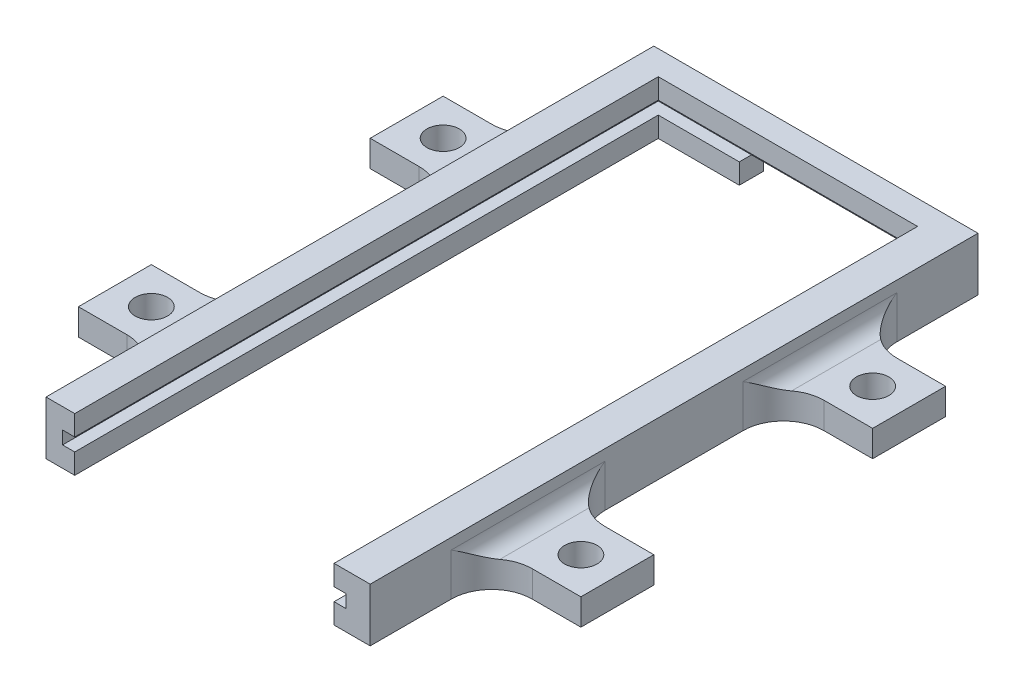
SolidWorks part; units mm, degrees
ref_plane "Front Plane" through (0, 0, 0) normal (0, 0, 1) x (1, 0, 0)
ref_plane "Top Plane" through (0, 0, 0) normal (0, 1, 0) x (1, 0, 0)
ref_plane "Right Plane" through (0, 0, 0) normal (1, 0, 0) x (0, 0, -1)
sketch "Sketch2" plane through (0, 0, 0) normal (0, 0, 1) x (1, 0, 0)
  line L1 (-20.1398, -2.4559) -> (19.8602, -2.4559)
  line L2 (-20.1398, -2.4559) -> (-20.1398, 4.1441)
  line L3 (-20.1398, 4.1441) -> (19.8602, 4.1441)
  line L4 (19.8602, -2.4559) -> (19.8602, 4.1441)
  point P0 (0, 0)
  dimension "D1" = 40
  dimension "D2" = 6.6
extrude "Boss-Extrude1" add sketch "Sketch2" along normal blind 3
sketch "Sketch3" plane through (0, 0, 3) normal (0, 0, 1) x (1, 0, 0)
  line L0 (-20.1398, -2.4559) -> (19.8602, -2.4559) construction
  line L1 (-18.0939, 1.6441) -> (16.9061, 1.6441)
  line L2 (-18.0939, 1.6441) -> (-18.0939, 0.0441)
  line L3 (-18.0939, 0.0441) -> (16.9061, 0.0441)
  line L4 (16.9061, 1.6441) -> (16.9061, 0.0441)
  point P0 (0, 0.8766)
  dimension "D1" = 35
  dimension "D2" = 1.6
  dimension "D3" = 2.5
extrude "Cut-Extrude1" cut sketch "Sketch3" against normal blind 1.5
sketch "Sketch4" plane through (0, 0, 3) normal (0, 0, 1) x (1, 0, 0)
  line L0 (-16.5939, 4.1441) -> (-20.1398, 4.1441)
  line L1 (19.8602, 4.1441) -> (-20.1398, 4.1441) construction
  line L2 (-20.1398, 4.1441) -> (-20.1398, -2.4559)
  line L3 (-20.1398, -2.4559) -> (-16.5939, -2.4559)
  line L4 (-20.1398, -2.4559) -> (19.8602, -2.4559) construction
  line L5 (-16.5939, -2.4559) -> (-16.5939, 0.0441)
  line L6 (-18.0939, 0.0441) -> (16.9061, 0.0441) construction
  line L7 (-16.5939, 0.0441) -> (-18.0939, 0.0441)
  line L8 (-18.0939, 0.0441) -> (-18.0939, 1.6441)
  line L9 (-18.0939, 1.6441) -> (-16.5939, 1.6441)
  line L10 (16.9061, 1.6441) -> (-18.0939, 1.6441) construction
  line L11 (-16.5939, 1.6441) -> (-16.5939, 4.1441)
  line L12 (15.4061, 4.1441) -> (15.4061, 1.6441)
  line L13 (15.4061, 1.6441) -> (16.9061, 1.6441)
  line L14 (16.9061, 1.6441) -> (16.9061, 0.0441)
  line L15 (16.9061, 0.0441) -> (15.4061, 0.0441)
  line L16 (-18.0939, 0.0441) -> (16.9061, 0.0441) construction
  line L17 (15.4061, 0.0441) -> (15.4061, -2.4559)
  line L18 (15.4061, -2.4559) -> (19.8602, -2.4559)
  line L19 (19.8602, -2.4559) -> (19.8602, 4.1441)
  line L20 (19.8602, 4.1441) -> (15.4061, 4.1441)
  dimension "D1" = 1.5
  dimension "D2" = 1.5
extrude "Boss-Extrude2" add sketch "Sketch4" along normal blind 72
sketch "Sketch5" plane through (0, 0, 3) normal (0, 0, 1) x (1, 0, 0)
  line L0 (-16.5939, 0.0441) -> (15.4061, 0.0441) construction
  line L1 (-6.5939, 0.0441) -> (15.4061, 0.0441)
  line L2 (-6.5939, 0.0441) -> (-6.5939, -2.4559)
  line L3 (-6.5939, -2.4559) -> (15.4061, -2.4559)
  line L4 (15.4061, 0.0441) -> (15.4061, -2.4559)
  line L5 (15.4061, 0.0441) -> (15.4061, -2.4559) construction
  line L6 (-16.5939, -2.4559) -> (15.4061, -2.4559) construction
  dimension "D1" = 22
extrude "Cut-Extrude2" cut sketch "Sketch5" against normal blind 4
sketch "Sketch6" plane through (-20.1398, 0, 0) normal (-1, 0, 0) x (0, 0, 1)
  line L0 (75, -2.4559) -> (0, -2.4559) construction
  line L1 (15, 0.7941) -> (24, 0.7941)
  line L2 (15, 0.7941) -> (15, -2.4559)
  line L3 (15, -2.4559) -> (24, -2.4559)
  line L4 (24, 0.7941) -> (24, -2.4559)
  line L5 (0, 4.1441) -> (0, -2.4559) construction
  line L6 (51, 0.7941) -> (60, 0.7941)
  line L7 (51, 0.7941) -> (51, -2.4559)
  line L8 (51, -2.4559) -> (60, -2.4559)
  line L9 (60, 0.7941) -> (60, -2.4559)
  line L10 (75, 4.1441) -> (75, -2.4559) construction
  dimension "D1" = 9
  dimension "D2" = 3.25
  dimension "D3" = 15
  dimension "D4" = 15
extrude "Boss-Extrude3" add sketch "Sketch6" along normal blind 11
sketch "Sketch7" plane through (19.8602, 0, 0) normal (1, 0, 0) x (0, 0, -1)
  line L0 (-75, -2.4559) -> (0, -2.4559) construction
  line L1 (-60, 0.7941) -> (-51, 0.7941)
  line L2 (-60, 0.7941) -> (-60, -2.4559)
  line L3 (-60, -2.4559) -> (-51, -2.4559)
  line L4 (-51, 0.7941) -> (-51, -2.4559)
  line L5 (-75, -2.4559) -> (-75, 4.1441) construction
  line L6 (-24, 0.7941) -> (-15, 0.7941)
  line L7 (-24, 0.7941) -> (-24, -2.4559)
  line L8 (-24, -2.4559) -> (-15, -2.4559)
  line L9 (-15, 0.7941) -> (-15, -2.4559)
  line L10 (0, -2.4559) -> (0, 4.1441) construction
  dimension "D1" = 9
  dimension "D2" = 3.25
  dimension "D3" = 15
  dimension "D4" = 15
extrude "Boss-Extrude4" add sketch "Sketch7" along normal blind 11
sketch "Sketch8" plane through (0, 0.7941, 0) normal (0, 1, 0) x (1, 0, 0)
  line L0 (-31.1398, -15) -> (-20.1398, -15) construction
  line L1 (-31.1398, -24) -> (-31.1398, -15) construction
  line L2 (-31.1398, -51) -> (-20.1398, -51) construction
  line L3 (-31.1398, -60) -> (-31.1398, -51) construction
  line L4 (30.8602, -15) -> (19.8602, -15) construction
  line L5 (30.8602, -15) -> (30.8602, -24) construction
  line L6 (30.8602, -51) -> (19.8602, -51) construction
  line L8 (30.8602, -51) -> (30.8602, -60) construction
  circle A0 centre (-26.6398, -19.5) radius 2
  circle A1 centre (-26.6398, -55.5) radius 2
  circle A2 centre (26.3602, -55.5) radius 2
  circle A3 centre (26.3602, -19.5) radius 2
  dimension "D1" = 4
  dimension "D4" = 4
  dimension "D5" = 4
  dimension "D6" = 4
  dimension "D2" = 4.5
  dimension "D3" = 4.5
  dimension "D7" = 4.5
  dimension "D8" = 4.5
  dimension "D9" = 4.5
  dimension "D10" = 4.5
  dimension "D11" = 4.5
  dimension "D12" = 4.5
extrude "Cut-Extrude3" cut sketch "Sketch8" against normal blind 3.25
fillet "Fillet1" radius 2 1 edges at (19.8602, 0.7941, 55.5)
fillet "Fillet2" radius 5 1 edges at (19.8602, 0.1691, 51)
fillet "Fillet3" radius 5 1 edges at (19.8602, 0.1691, 60)
fillet "Fillet4" radius 2 1 edges at (19.8602, 0.7941, 19.5)
fillet "Fillet5" radius 5 1 edges at (19.8602, 0.1691, 15)
fillet "Fillet6" radius 5 1 edges at (19.8602, 0.1691, 24)
fillet "Fillet7" radius 2 1 edges at (-20.1398, 0.7941, 55.5)
fillet "Fillet8" radius 2 1 edges at (-20.1398, 0.7941, 19.5)
fillet "Fillet9" radius 5 1 edges at (-20.1398, 0.1691, 15)
fillet "Fillet10" radius 5 1 edges at (-20.1398, 0.1691, 24)
fillet "Fillet11" radius 5 1 edges at (-20.1398, 0.1691, 51)
fillet "Fillet12" radius 5 1 edges at (-20.1398, 0.1691, 60)
